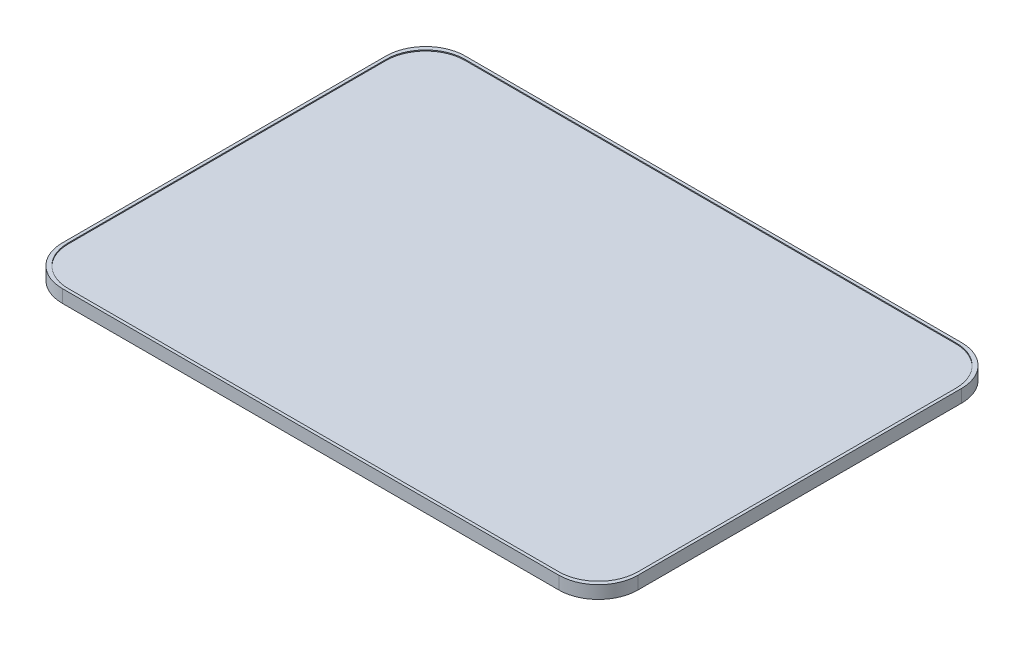
SolidWorks part; units mm, degrees
ref_plane "Front Plane" through (0, 0, 0) normal (0, 0, 1) x (1, 0, 0)
ref_plane "Top Plane" through (0, 0, 0) normal (0, 1, 0) x (1, 0, 0)
ref_plane "Right Plane" through (0, 0, 0) normal (1, 0, 0) x (0, 0, -1)
sketch "Sketch1" plane through (0, 0, 0) normal (0, 1, 0) x (1, 0, 0)
  line L1 (-291.5, -204) -> (291.5, -204)
  line L2 (-291.5, -204) -> (-291.5, 204)
  line L3 (-291.5, 204) -> (291.5, 204)
  line L4 (291.5, -204) -> (291.5, 204)
  line L5 (-291.5, -204) -> (291.5, 204) construction
  line L6 (-291.5, 204) -> (291.5, -204) construction
  point P0 (0, 0)
  dimension "D1" = 583
  dimension "D2" = 408
extrude "Boss-Extrude1" add sketch "Sketch1" along normal blind 11
sketch "Sketch2" plane through (0, 11, 0) normal (0, 1, 0) x (1, 0, 0)
  line L1 (288.5, -201) -> (-288.5, -201)
  line L2 (288.5, -201) -> (288.5, 201)
  line L3 (288.5, 201) -> (-288.5, 201)
  line L4 (-288.5, -201) -> (-288.5, 201)
  line L5 (288.5, -201) -> (-288.5, 201) construction
  line L6 (288.5, 201) -> (-288.5, -201) construction
  line L7 (291.5, -204) -> (-291.5, -204)
  line L8 (291.5, -204) -> (291.5, 204)
  line L9 (291.5, 204) -> (-291.5, 204)
  line L10 (-291.5, -204) -> (-291.5, 204)
  line L11 (291.5, -204) -> (-291.5, 204) construction
  line L12 (291.5, 204) -> (-291.5, -204) construction
  point P0 (0, 0)
  point P6 (0, 0)
  dimension "D1" = 3
  dimension "D2" = 3
extrude "Boss-Extrude2" add sketch "Sketch2" along normal blind 1
sketch "Sketch3" plane through (0, 0, 0) normal (0, -1, 0) x (1, 0, 0)
  line L1 (291.5, -204) -> (-291.5, -204)
  line L2 (291.5, -204) -> (291.5, 204)
  line L3 (291.5, 204) -> (-291.5, 204)
  line L4 (-291.5, -204) -> (-291.5, 204)
  line L5 (291.5, -204) -> (-291.5, 204) construction
  line L6 (291.5, 204) -> (-291.5, -204) construction
  line L7 (288.5, -201) -> (-288.5, -201)
  line L8 (288.5, -201) -> (288.5, 201)
  line L9 (288.5, 201) -> (-288.5, 201)
  line L10 (-288.5, -201) -> (-288.5, 201)
  line L11 (288.5, -201) -> (-288.5, 201) construction
  line L12 (288.5, 201) -> (-288.5, -201) construction
  point P0 (0, 0)
  point P7 (0, 0)
  dimension "D1" = 3
  dimension "D2" = 3
extrude "Boss-Extrude3" add sketch "Sketch3" along normal blind 1
fillet "Fillet2" radius 40 12 edges at (-288.5, -0.5, 201) (288.5, -0.5, -201) (-288.5, -0.5, -201) (-291.5, 5.5, -204) (291.5, 5.5, -204) (-291.5, 5.5, 204) (-288.5, 11.5, 201) (288.5, 11.5, -201) (-288.5, 11.5, -201) (288.5, -0.5, 201) (288.5, 11.5, 201) (291.5, 5.5, 204)
sketch "Sketch4" plane through (0, 0, 0) normal (0, -1, 0) x (1, 0, 0)
  line L0 (-276.7843, 189.2843) -> (276.7843, -189.2843) construction
  line L1 (276.7843, 189.2843) -> (-276.7843, -189.2843) construction
  line L11 (-288.5, 0) -> (-288.5, 201) construction
  line L12 (-288.5, 100.5) -> (-144.25, 100.5) construction
  line L13 (-144.25, 201) -> (-144.25, 100.5) construction
  line L14 (0, 201) -> (-288.5, 201) construction
  arc A0 (-248.5, 201) -> (-288.5, 161) centre (-248.5, 161) ccw construction
  arc A1 (248.5, -201) -> (288.5, -161) centre (248.5, -161) ccw construction
  arc A2 (288.5, 161) -> (248.5, 201) centre (248.5, 161) ccw construction
  arc A3 (-288.5, -161) -> (-248.5, -201) centre (-248.5, -161) ccw construction
